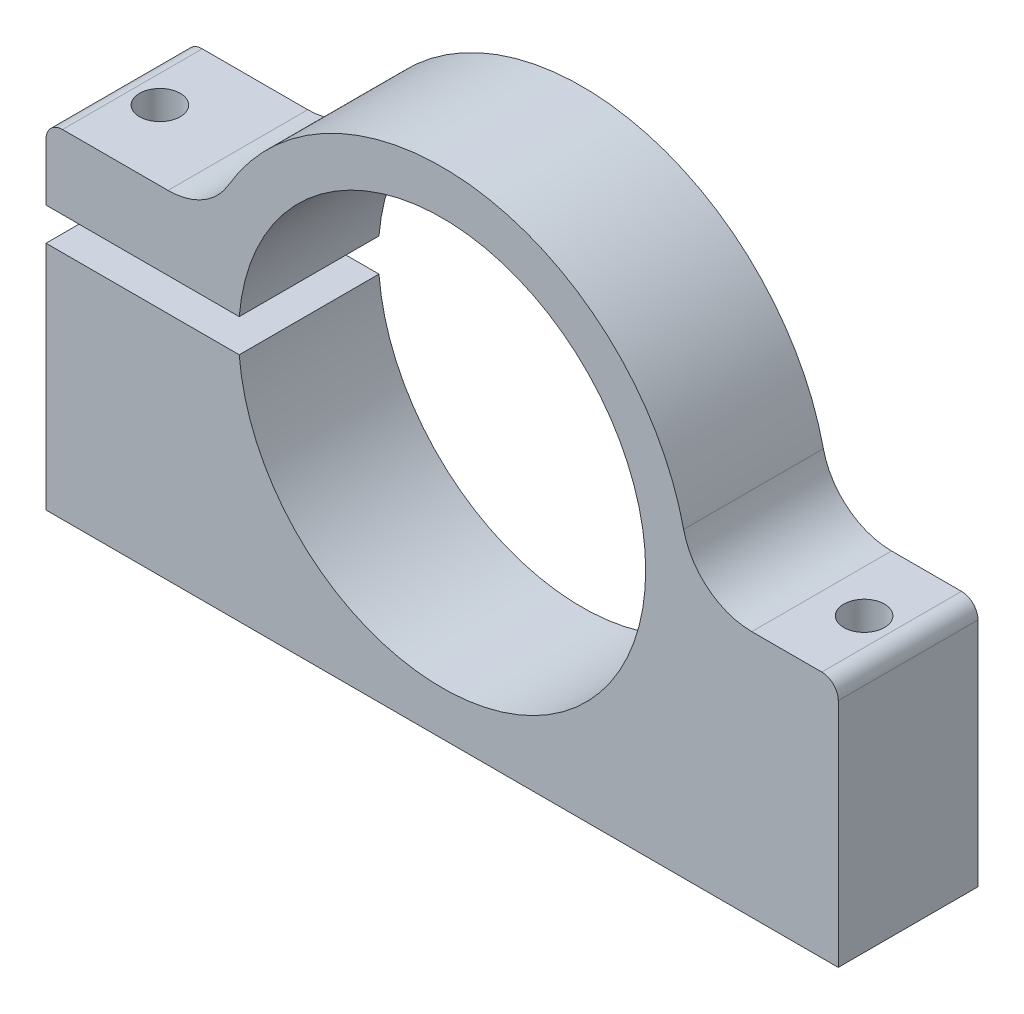
SolidWorks part; units mm, degrees
material "2024 Alloy"
ref_plane "Front Plane" through (0, 0, 0) normal (0, 0, 1) x (1, 0, 0)
ref_plane "Top Plane" through (0, 0, 0) normal (0, 1, 0) x (1, 0, 0)
ref_plane "Right Plane" through (0, 0, 0) normal (1, 0, 0) x (0, 0, -1)
ref_plane "Plane1" through (0, 0, 6.35) normal (0, 0, 1) x (1, 0, 0)
sketch "Sketch1" plane through (0, 0, 6.35) normal (0, 0, 1) x (1, 0, 0)
  line L0 (-20.9526, 8.2) -> (-36, 8.2)
  line L1 (-36, 8.2) -> (-36, -22.5)
  line L2 (-36, -22.5) -> (36, -22.5)
  line L3 (36, -22.5) -> (36, 0)
  line L4 (36, 0) -> (22.5, 0)
  arc A0 (22.5, 0) -> (-20.9526, 8.2) centre (0, 0) ccw
extrude "Boss-Extrude1" add sketch "Sketch1" against normal blind 12.7
sketch "Sketch2" plane through (0, 0, -6.35) normal (0, 0, -1) x (-1, 0, 0)
  line L0 (36, 1.5) -> (18.4391, 1.5)
  line L1 (18.4391, -1.5) -> (36, -1.5)
  line L2 (36, -1.5) -> (36, 1.5)
  arc A0 (18.4391, 1.5) -> (18.4391, -1.5) centre (0, 0) cw
extrude "Cut-Extrude1" cut sketch "Sketch2" against normal through all
sketch "Sketch3" plane through (0, 0, 0) normal (0, 1, 0) x (1, 0, 0)
  line L0 (18.5, 6.35) -> (0, 6.35)
  line L1 (0, 6.35) -> (0, -6.35)
  line L2 (0, -6.35) -> (18.5, -6.35)
  line L3 (18.5, -6.35) -> (18.5, 6.35)
  line L4 (0, 6.35) -> (0, -6.35) construction
revolve "Cut-Revolve1" cut sketch "Sketch3" angle 360 about L4
hole_wizard "Ø3.7 (3.7) Diameter Hole1" positions "Sketch5" profile "Sketch4" hole size "Ø3.7" standard "ANSI Metric"
sketch "Sketch5" plane through (0, 8.2, 0) normal (0, 1, 0) x (1, 0, 0)
  point P0 (-32, 0)
sketch "Sketch4" plane through (-32, 8.2, 0) normal (1, 0, 0) x (0, 0, 1)
  line L0 (0, 0) -> (0, 6.7)
  line L1 (0, 6.7) -> (1.85, 6.7)
  line L2 (1.85, 6.7) -> (1.85, 0)
  line L5 (1.85, 0) -> (0, 0)
  line L11 (0, -6.35) -> (0, 107.95) construction
  dimension "Thru Hole Dia." = 3.7
  dimension "Thru Hole Depth" = 6.7
hole_wizard "Ø3.7 (3.7) Diameter Hole2" positions "Sketch7" profile "Sketch6" hole size "Ø3.7" standard "ANSI Metric"
sketch "Sketch7" plane through (0, -22.5, 0) normal (0, -1, 0) x (-1, 0, 0)
  point P0 (32, 0)
sketch "Sketch6" plane through (-32, -22.5, 0) normal (1, 0, 0) x (0, 0, -1)
  line L0 (0, 0) -> (0, 45)
  line L1 (0, 45) -> (1.85, 45)
  line L2 (1.85, 45) -> (1.85, 0)
  line L5 (1.85, 0) -> (0, 0)
  line L11 (0, -6.35) -> (0, 107.95) construction
  dimension "Thru Hole Dia." = 3.7
  dimension "Thru Hole Depth" = 45
hole_wizard "Ø3.7 (3.7) Diameter Hole3" positions "Sketch9" profile "Sketch8" hole size "Ø3.7" standard "ANSI Metric"
sketch "Sketch9" plane through (0, -22.5, 0) normal (0, -1, 0) x (-1, 0, 0)
  point P0 (-32, 0)
sketch "Sketch8" plane through (32, -22.5, 0) normal (1, 0, 0) x (0, 0, -1)
  line L0 (0, 0) -> (0, 45)
  line L1 (0, 45) -> (1.85, 45)
  line L2 (1.85, 45) -> (1.85, 0)
  line L5 (1.85, 0) -> (0, 0)
  line L11 (0, -6.35) -> (0, 107.95) construction
  dimension "Thru Hole Dia." = 3.7
  dimension "Thru Hole Depth" = 45
fillet "Fillet1" radius 1.5 2 edges at (-36, 8.2, 0) (36, 0, 0)
fillet "Fillet2" radius 6.35 2 edges at (-20.9526, 8.2, 0) (22.5, 0, 0)
